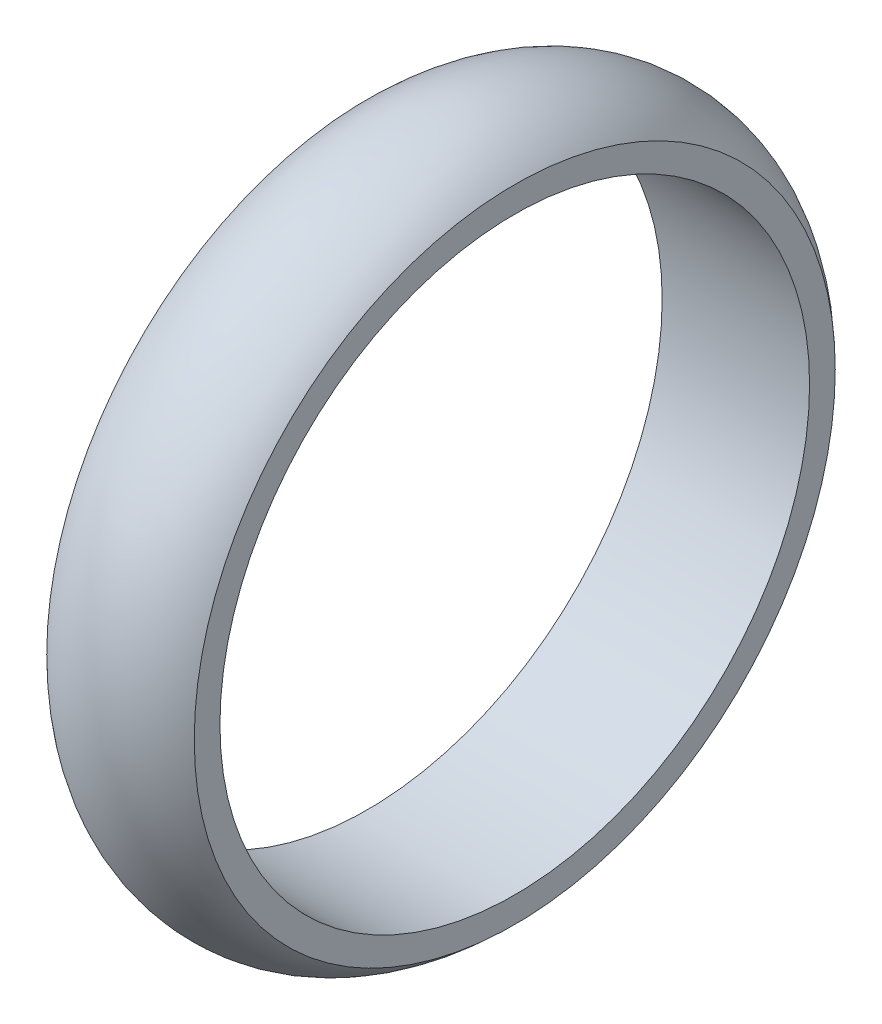
SolidWorks part; units mm, degrees
material "POLIURETANO (11671)"
ref_plane "Alzado" through (0, 0, 0) normal (0, 0, 1) x (1, 0, 0)
ref_plane "Planta" through (0, 0, 0) normal (0, 1, 0) x (1, 0, 0)
ref_plane "Vista lateral" through (0, 0, 0) normal (1, 0, 0) x (0, 0, -1)
sketch "Croquis1" plane through (0, 0, 0) normal (1, 0, 0) x (0, 0, -1)
  line L0 (0, 0) -> (0, 228.6) construction
  dimension "D1" = 228.6
sketch "Croquis2" plane through (0, 0, 0) normal (0, 0, 1) x (1, 0, 0)
  line L0 (-57.15, 228.6) -> (57.15, 228.6) construction
  line L2 (0, 0) -> (0, 228.6) construction
  line L3 (-57.15, 228.6) -> (-57.15, 248.6)
  line L4 (57.15, 228.6) -> (57.15, 248.5148)
  line L5 (-57.15, 228.6) -> (57.15, 228.6)
  arc A0 (57.15, 248.5148) -> (-57.15, 248.6) centre (-0.0426, 191.4074) ccw
  point P4 (0, 228.6)
  dimension "D1" = 114.3
  dimension "D2" = 20
sketch "Croquis5" plane through (0, 0, 0) normal (0, 0, 1) x (1, 0, 0)
  line L0 (-19.7853, 0) -> (30.9266, 0) construction
revolve "Revolución1" add sketch "Croquis2" angle 360 about L0
